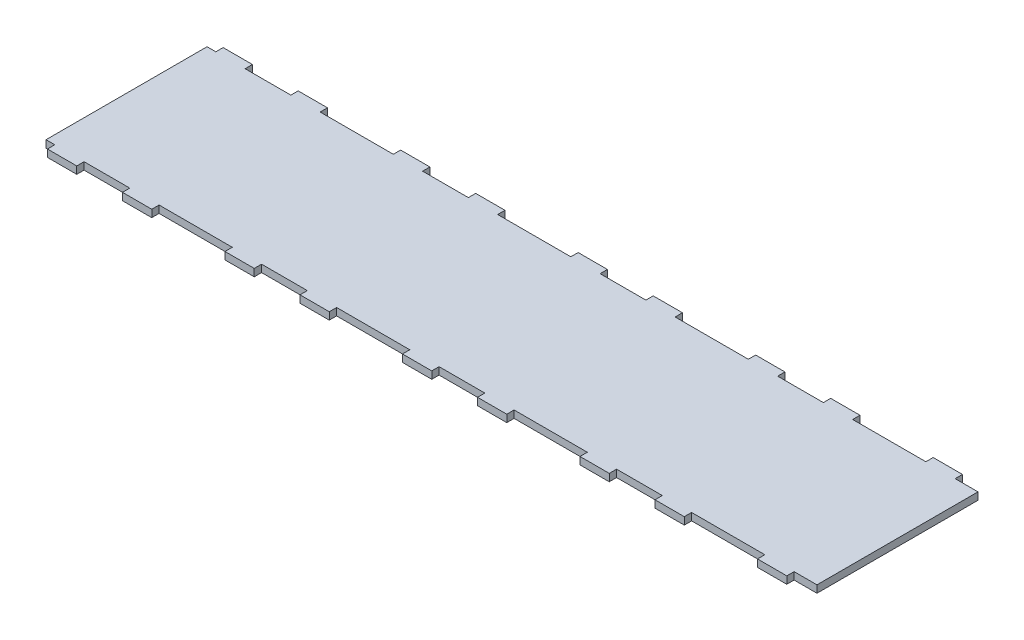
SolidWorks part; units mm, degrees
material "Cedar"
ref_plane "Front Plane" through (0, 0, 0) normal (0, 0, 1) x (1, 0, 0)
ref_plane "Top Plane" through (0, 0, 0) normal (0, 1, 0) x (1, 0, 0)
ref_plane "Right Plane" through (0, 0, 0) normal (1, 0, 0) x (0, 0, -1)
sketch "Sketch1" plane through (0, 0, 0) normal (0, 1, 0) x (1, 0, 0)
  line L1 (-360.8183, 76.2) -> (360.8183, 76.2)
  line L2 (-360.8183, 76.2) -> (-360.8183, -76.2)
  line L3 (-360.8183, -76.2) -> (360.8183, -76.2)
  line L4 (360.8183, 76.2) -> (360.8183, -76.2)
  line L5 (-360.8183, 76.2) -> (360.8183, -76.2) construction
  line L6 (-360.8183, -76.2) -> (360.8183, 76.2) construction
  point P0 (0, 0)
  dimension "D1" = 721.6366
  dimension "D2" = 152.4
extrude "Boss-Extrude1" add sketch "Sketch1" along normal blind 6.35
sketch "Sketch2" plane through (0, 6.35, 0) normal (0, 1, 0) x (1, 0, 0)
  line L0 (0, -76.2) -> (0, -69.85) construction
  line L1 (-32.5397, -69.85) -> (32.5397, -69.85) construction
  line L2 (-45.2397, -69.85) -> (-19.8397, -69.85) construction
  line L3 (-45.2397, -69.85) -> (-45.2397, -76.2) construction
  line L4 (-45.2397, -76.2) -> (-19.8397, -76.2) construction
  line L5 (-19.8397, -69.85) -> (-19.8397, -76.2)
  line L6 (-45.2397, -69.85) -> (-19.8397, -76.2) construction
  line L7 (-45.2397, -76.2) -> (-19.8397, -69.85) construction
  line L8 (-360.8183, -76.2) -> (360.8183, -76.2) construction
  line L9 (-19.8397, -69.85) -> (19.8397, -69.85)
  line L10 (19.8397, -69.85) -> (45.2397, -69.85) construction
  line L11 (19.8397, -69.85) -> (19.8397, -76.2)
  line L12 (19.8397, -76.2) -> (45.2397, -76.2) construction
  line L13 (45.2397, -69.85) -> (45.2397, -76.2) construction
  line L14 (19.8397, -69.85) -> (45.2397, -76.2) construction
  line L15 (19.8397, -76.2) -> (45.2397, -69.85) construction
  line L16 (19.8397, -76.2) -> (-19.8397, -76.2)
  line L17 (-45.2397, -76.2) -> (-45.2397, -69.85)
  line L18 (-45.2397, -69.85) -> (-76.9897, -69.85)
  line L19 (-76.9897, -69.85) -> (-76.9897, -76.2)
  line L20 (-76.9897, -76.2) -> (-45.2397, -76.2)
  line L21 (45.2397, -69.85) -> (76.9897, -69.85)
  line L22 (76.9897, -69.85) -> (76.9897, -76.2)
  line L23 (76.9897, -76.2) -> (45.2397, -76.2)
  line L24 (45.2397, -76.2) -> (45.2397, -69.85)
  point P5 (0, -69.85)
  point P6 (-32.5397, -73.025)
  point P11 (-32.5397, -69.85)
  point P17 (32.5397, -73.025)
  point P24 (32.5397, -69.85)
  dimension "D1" = 39.6793
  dimension "D2" = 25.4
  dimension "D3" = 6.35
  dimension "D4" = 76.9897
  dimension "D5" = 25.4
  dimension "D6" = 6.35
  dimension "D7" = 76.9897
extrude "Cut-Extrude1" cut sketch "Sketch2" against normal through all
pattern_linear "LPattern1" count 3 spacing 153.9793 along (1, 0, 0) count 3 spacing 153.9793 along (-1, 0, 0) of "Cut-Extrude1"
mirror "Mirror1" about plane through (0, 0, 0) normal (0, 0, 1) of "LPattern1", "Cut-Extrude1"
sketch "Sketch3" plane through (0, 6.35, 0) normal (0, 1, 0) x (1, 0, 0)
  line L0 (307.9586, 69.85) -> (307.9586, -76.2)
  line L1 (327.7983, 69.85) -> (288.119, 69.85) construction
  line L2 (307.9586, -76.2) -> (360.8183, -76.2)
  line L3 (360.8183, -76.2) -> (360.8183, 76.2)
  line L4 (360.8183, 76.2) -> (307.9586, 76.2)
  line L5 (307.9586, 76.2) -> (307.9586, 69.85)
extrude "Cut-Extrude2" cut sketch "Sketch3" against normal through all
